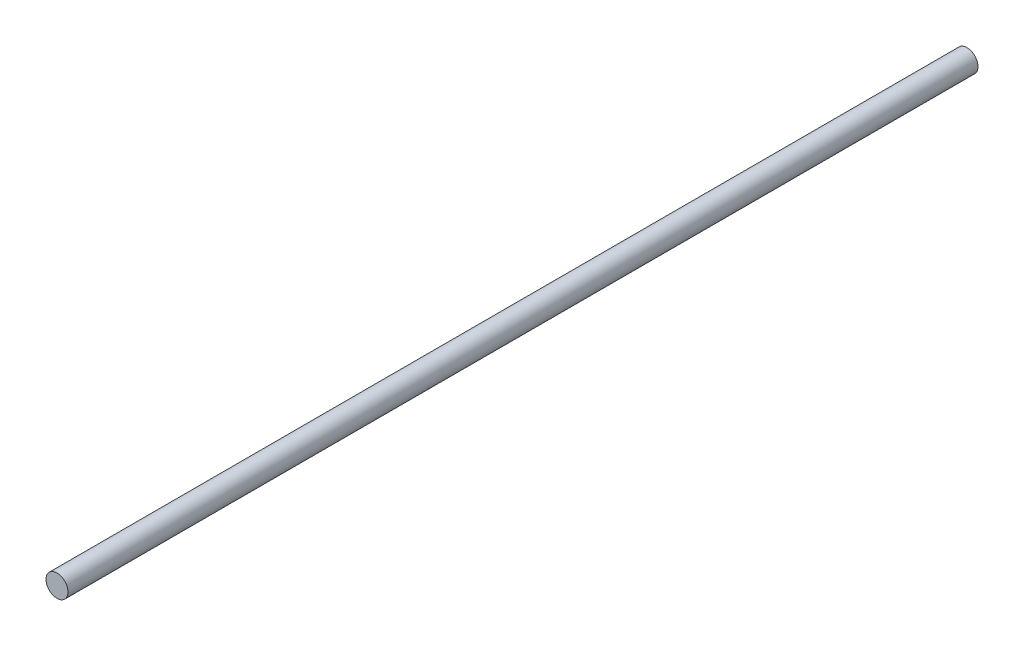
SolidWorks part; units mm, degrees
ref_plane "Front Plane" through (0, 0, 0) normal (0, 0, 1) x (1, 0, 0)
ref_plane "Top Plane" through (0, 0, 0) normal (0, 1, 0) x (1, 0, 0)
ref_plane "Right Plane" through (0, 0, 0) normal (1, 0, 0) x (0, 0, -1)
sketch "Sketch1" plane through (0, 0, 0) normal (0, 0, 1) x (1, 0, 0)
  circle A0 centre (0, 0) radius 0.75
  dimension "D1" = 1.5
extrude "Boss-Extrude1" add sketch "Sketch1" along normal blind 62
